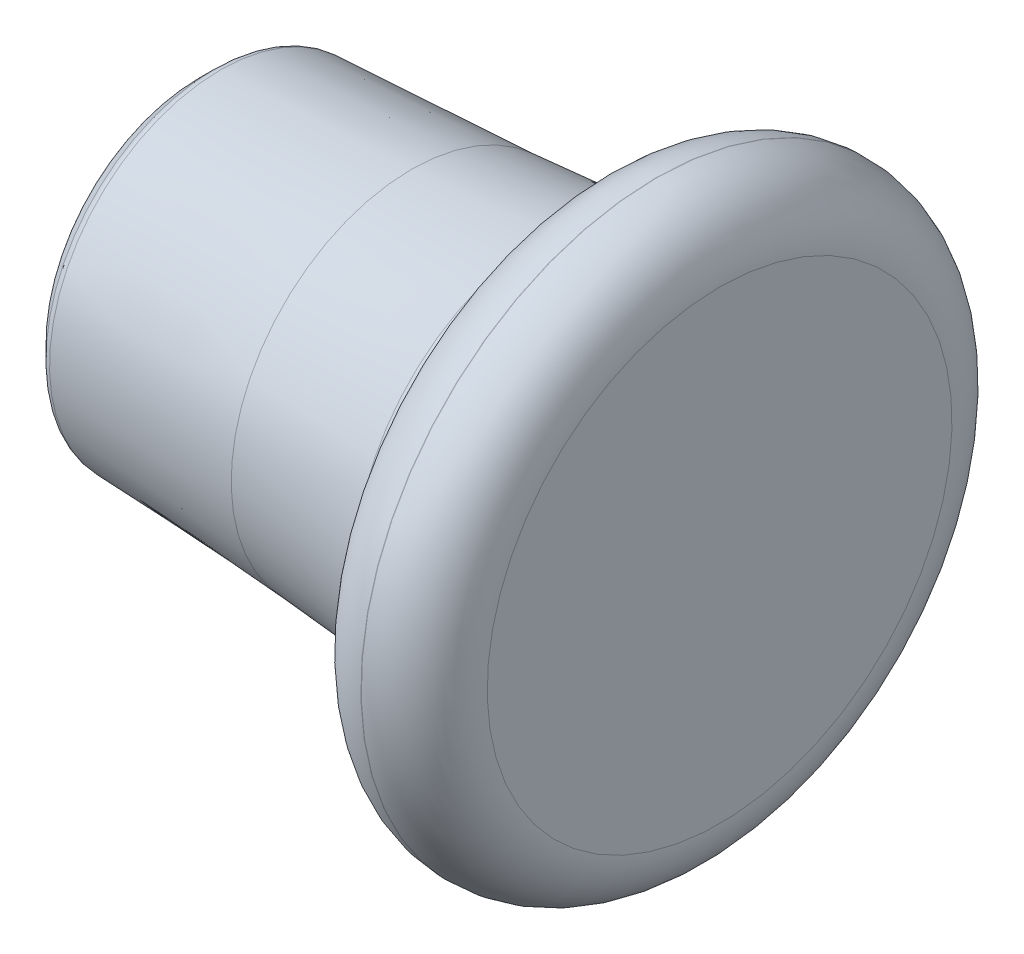
SolidWorks part; units mm, degrees
ref_plane "Front Plane" through (0, 0, 0) normal (0, 0, 1) x (1, 0, 0)
ref_plane "Top Plane" through (0, 0, 0) normal (0, 1, 0) x (1, 0, 0)
ref_plane "Right Plane" through (0, 0, 0) normal (1, 0, 0) x (0, 0, -1)
sketch "Sketch2" plane through (0, 0, 0) normal (0, 0, 1) x (1, 0, 0)
  line L1 (-127.7289, 81.725) -> (0.2711, 81.725) construction
  line L2 (-16, 50) -> (-16, 66) construction
  line L3 (-126.767, 81.6769) -> (-78.2289, 79.25)
  line L4 (0, 78.5) -> (0, 125)
  line L5 (-132.7289, 87.7605) -> (-132.7289, 97.7605)
  line L6 (-132.7289, 87.7605) -> (-132.7289, 97.7605)
  line L9 (-131.9967, 85.9928) -> (-128.41, 82.406)
  line L10 (0, 78.5) -> (0, 66)
  line L11 (-16, 50) -> (-16.0989, 50)
  line L13 (-16, 66) -> (-16.0989, 66)
  line L14 (-63.2289, 78.5) -> (0, 78.5) construction
  line L15 (-16.0989, 66) -> (-16.0989, 50) construction
  line L16 (-32.4125, 63) -> (2.5331, 63) construction
  line L17 (-31.8152, 63) -> (-31.8152, 77.3563) construction
  line L18 (-16.0989, 50) -> (-16, 50)
  line L19 (-132.7289, 92.7605) -> (-118.3038, 92.7605) construction
  line L20 (-32.0568, 63.6638) -> (-32.7542, 65.5799)
  line L21 (-63.2289, 77.2076) -> (-48.7289, 77.2076) construction
  line L22 (-48.7289, 77.2076) -> (-48.7289, 76.3083) construction
  line L23 (-48.7289, 76.3083) -> (-48.7289, 56.553) construction
  line L24 (-128.41, 82.406) -> (-128.41, 125) construction
  line L30 (-132.7289, 97.7605) -> (-132.7289, 125)
  line L31 (-133, 150) -> (-132.7289, 150) construction
  line L39 (-132.7289, 150) -> (-133, 150)
  line L42 (-16, 50) -> (-16, 125)
  line L43 (0, 125) -> (-132.7289, 125)
  arc A0 (-16, 50) -> (0, 66) centre (-16, 66) ccw
  arc A1 (-31.7019, 62.4576) -> (-16.0989, 50) centre (-16.0989, 66) ccw
  arc A4 (-32.7542, 65.5799) -> (-39.1693, 73.823) centre (-48.7289, 59.7655) ccw
  arc A5 (-43.123, 75.4135) -> (-78.2289, 79.25) centre (-93.2102, -220.3757) ccw
  arc A7 (-31.7019, 62.4576) -> (-32.0568, 63.6638) centre (-41.4537, 60.2436) ccw
  arc A8 (-39.1693, 73.823) -> (-43.123, 75.4135) centre (-44.7926, 65.5539) ccw
  arc A9 (-131.9967, 85.9928) -> (-132.7289, 87.7605) centre (-130.2289, 87.7605) cw
  arc A10 (-126.767, 81.6769) -> (-128.41, 82.406) centre (-126.6422, 84.1738) cw
  point P8 (0, 0)
  point P23 (0, 0)
  dimension "D6" = 2.862
  dimension "D3" = 13
  dimension "D2" = 32
  dimension "D4" = 48.5381
  dimension "D5" = 10
  dimension "D8" = 35.1059
  dimension "D9" = 34
  dimension "D10" = 10
  dimension "D11" = 2.5
  dimension "D12" = 2.5
  dimension "D13" = 300
  dimension "D14" = 16.0989
  dimension "D15" = 15.6029
  dimension "D17" = 132.7289
  dimension "D7" = 10
  dimension "D16" = 11.4212
revolve "Revolve1" add sketch "Sketch2" angle 360 about L43
